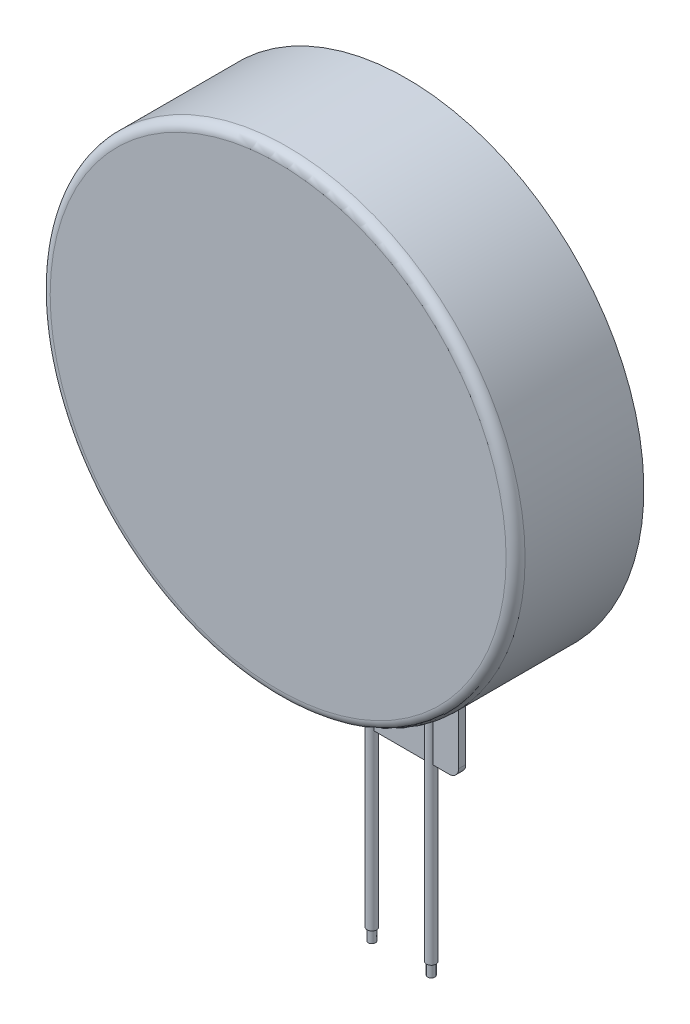
SolidWorks part; units mm, degrees
ref_plane "Front" through (0, 0, 0) normal (0, 0, 1) x (1, 0, 0)
ref_plane "Top" through (0, 0, 0) normal (0, 1, 0) x (1, 0, 0)
ref_plane "Right" through (0, 0, 0) normal (1, 0, 0) x (0, 0, -1)
sketch "Sketch1" plane through (0, 0, 0) normal (0, 0, 1) x (1, 0, 0)
  circle A0 centre (0, 0) radius 5
  dimension "D1" = 10
extrude "Boss-Extrude1" add sketch "Sketch1" along normal blind 2.7
sketch "Sketch2" plane through (0, 0, 0) normal (0, 0, -1) x (-1, 0, 0)
  line L0 (0, -5.7832) -> (0, 5.8717) construction
sketch "Sketch3" plane through (0, 0, 0) normal (0, 0, -1) x (-1, 0, 0)
  line L0 (1.25, -4.8412) -> (1.25, -7.0912)
  line L1 (-1.25, -4.8412) -> (-1.25, -7.0912)
  line L2 (0, -5.7832) -> (0, 5.8717) construction
  line L3 (1.25, -7.0912) -> (-1.25, -7.0912)
  line L4 (1.25, -4.8412) -> (1.25, -4.1797)
  line L5 (1.25, -4.1797) -> (-1.25, -4.1797)
  line L6 (-1.25, -4.1797) -> (-1.25, -4.8412)
  dimension "D2" = 1.25
  dimension "D3" = 1.25
  dimension "D4" = 2.25
extrude "Boss-Extrude2" add sketch "Sketch3" against normal blind 0.15
sketch "Sketch4" plane through (0, -7.0912, 0) normal (0, -1, 0) x (1, 0, 0)
  line L0 (1.25, 0) -> (-1.25, 0) construction
  circle A0 centre (-0.625, 0.101) radius 0.101
  circle A1 centre (0.625, 0.101) radius 0.101
  dimension "D1" = 0.202
  dimension "D2" = 0.202
  dimension "D3" = 0.625
  dimension "D4" = 0.625
  dimension "D5" = 0.101
  dimension "D6" = 0.101
extrude "Boss-Extrude3" add sketch "Sketch4" along normal blind 3.9 and the other way blind 2.2 separate body
fillet "Fillet1" radius 0.2 2 edges at (-1.25, -7.0912, 0.075) (1.25, -7.0912, 0.075)
fillet "Fillet2" radius 0.2 1 edges at (5, 0, 2.7)
sketch "Sketch5" plane through (0, -10.9912, 0) normal (0, -1, 0) x (1, 0, 0)
  circle A1 centre (-0.625, 0.101) radius 0.075
  circle A2 centre (0.625, 0.101) radius 0.075
  dimension "D1" = 0.15
  dimension "D2" = 0.15
extrude "Cut-Extrude4" cut sketch "Sketch5" against normal blind 0.25 flip side to cut
